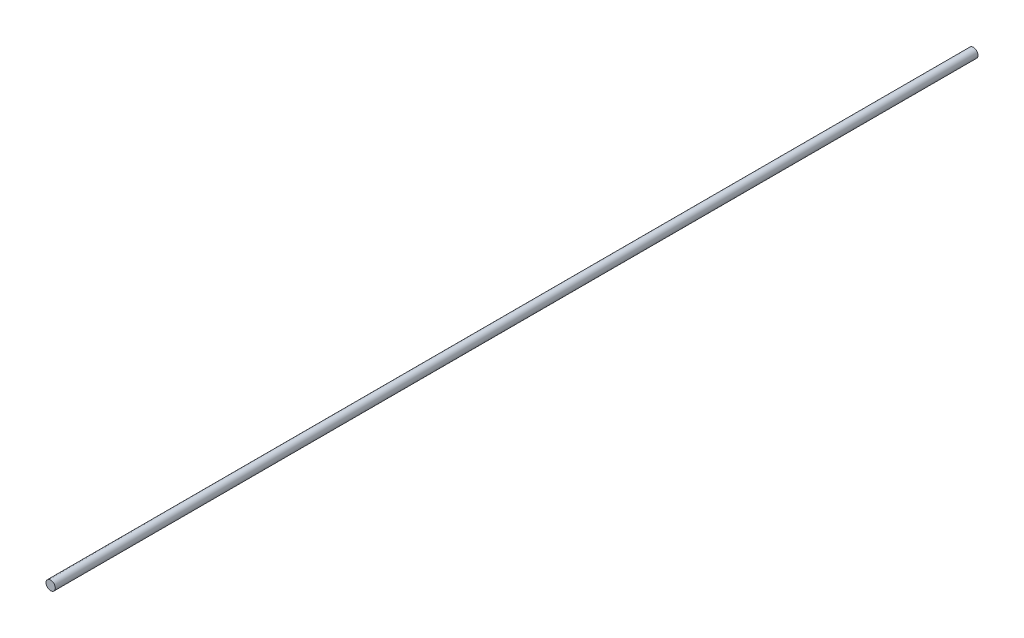
SolidWorks part; units mm, degrees
ref_plane "Front Plane" through (0, 0, 0) normal (0, 0, 1) x (1, 0, 0)
ref_plane "Top Plane" through (0, 0, 0) normal (0, 1, 0) x (1, 0, 0)
ref_plane "Right Plane" through (0, 0, 0) normal (1, 0, 0) x (0, 0, -1)
sketch "Sketch1" plane through (0, 0, 0) normal (0, 0, 1) x (1, 0, 0)
  circle A0 centre (0, 0) radius 1.5875
extrude "Boss-Extrude1" add sketch "Sketch1" along normal blind 315.468
